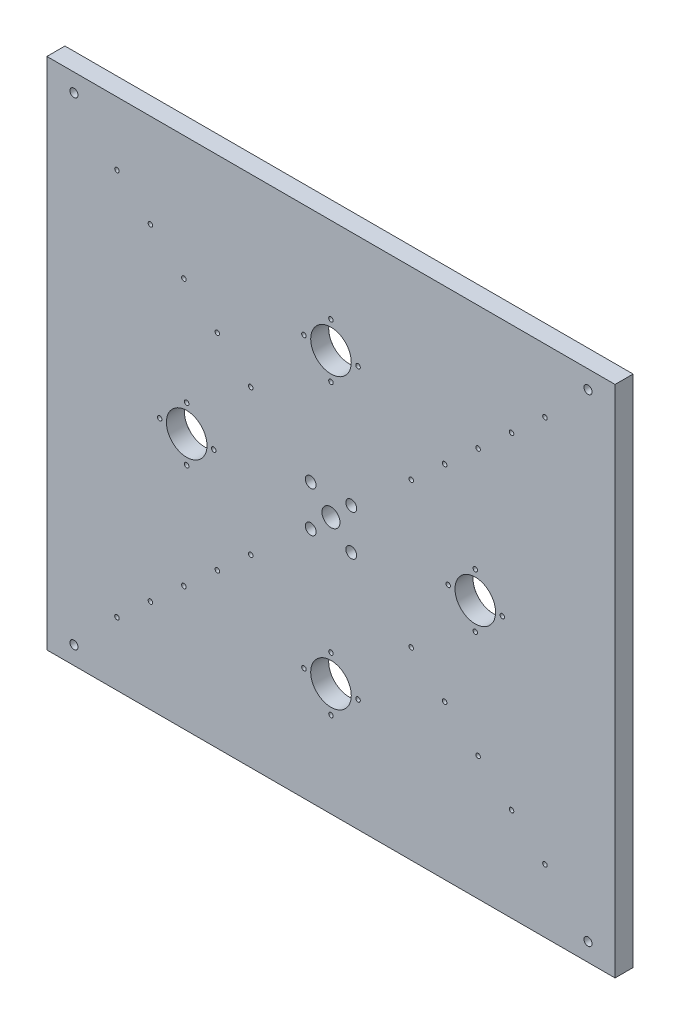
SolidWorks part; units mm, degrees
ref_plane "前视基准面" through (0, 0, 0) normal (0, 0, 1) x (1, 0, 0)
ref_plane "上视基准面" through (0, 0, 0) normal (0, 1, 0) x (1, 0, 0)
ref_plane "右视基准面" through (0, 0, 0) normal (1, 0, 0) x (0, 0, -1)
sketch "草图1" plane through (0, 0, 0) normal (0, 0, 1) x (1, 0, 0)
  line L1 (-315, 285) -> (315, 285)
  line L2 (-315, 285) -> (-315, -285)
  line L3 (-315, -285) -> (315, -285)
  line L4 (315, 285) -> (315, -285)
  line L5 (-315, 285) -> (315, -285) construction
  line L6 (-315, -285) -> (315, 285) construction
  point P0 (0, 0)
  dimension "D1" = 630
  dimension "D2" = 570
extrude "凸台-拉伸1" add sketch "草图1" along normal blind 20
hole_wizard "大小mm 暗销槽口2" positions "草图2" profile "草图3" size "Ø20.0" standard "GB" slot yes
sketch "草图2" plane through (0, 0, 0) normal (0, 0, -1) x (-1, 0, 0)
  point P0 (0, 0)
sketch "草图3" plane through (0, 0, 0) normal (1, 0, 0) x (0, 1, 0)
  line L0 (0, 0) -> (0, 26.0086)
  line L1 (0, 26.0086) -> (10, 20)
  line L2 (10, 20) -> (10, 0.025)
  line L3 (10, 0.025) -> (10.025, 0)
  line L5 (10.025, 0) -> (0, 0)
  line L6 (-10, 0.025) -> (-10.025, 0) construction
  line L10 (0, 26.0086) -> (-10, 20) construction
  line L11 (0, -6.35) -> (0, 107.95) construction
  dimension "孔直径" = 20
  dimension "孔深度" = 20
  dimension "近端锥形沉头孔直径" = 20.05
  dimension "近端锥形沉头孔角度" = 90
  dimension "导头角度" = 118
sketch "草图4" plane through (0, 0, 0) normal (0, 0, -1) x (-1, 0, 0)
  line L0 (-315, -285) -> (315, 285) construction
  line L1 (-22.5, 22.5) -> (22.5, 22.5)
  line L2 (-22.5, 22.5) -> (-22.5, -22.5)
  line L3 (-22.5, -22.5) -> (22.5, -22.5)
  line L4 (22.5, 22.5) -> (22.5, -22.5)
  line L5 (-22.5, 22.5) -> (22.5, -22.5) construction
  line L6 (-22.5, -22.5) -> (22.5, 22.5) construction
  line L7 (-315, 285) -> (315, -285) construction
  line L8 (315, -285) -> (-315, -285) construction
  line L9 (315, 285) -> (315, -285) construction
  line L10 (-237.2914, -214.6923) -> (-88.9843, -80.5096)
  line L11 (-160, 0) -> (160, 0) construction
  line L12 (0, 160) -> (0, -160) construction
  line L13 (-237.2914, 214.6923) -> (-88.9843, 80.5096)
  line L14 (237.2914, -214.6923) -> (88.9843, -80.5096)
  line L15 (237.2914, 214.6923) -> (88.9843, 80.5096)
  line L16 (-160, 0) -> (0, -160)
  line L17 (-285, 265) -> (285, 265)
  line L18 (-285, 265) -> (-285, -265)
  line L19 (-285, -265) -> (285, -265)
  line L20 (285, 265) -> (285, -265)
  line L21 (-285, 265) -> (285, -265) construction
  line L22 (-285, -265) -> (285, 265) construction
  line L23 (-160, 0) -> (0, 160)
  line L24 (0, -160) -> (160, 0)
  line L25 (0, 160) -> (160, 0)
  circle A0 centre (160, 0) radius 30
  circle A1 centre (0, -160) radius 30
  point P0 (0, 0)
  point P8 (160, 30)
  point P25 (-200.2147, -181.1466)
  point P26 (-163.1379, -147.6009)
  point P27 (-126.0611, -114.0553)
  point P28 (130, 0)
  point P30 (-126.0611, 114.0553)
  point P31 (-163.1379, 147.6009)
  point P32 (-200.2147, 181.1466)
  point P35 (126.0611, -114.0553)
  point P36 (163.1379, -147.6009)
  point P37 (200.2147, -181.1466)
  point P40 (200.2147, 181.1466)
  point P41 (163.1379, 147.6009)
  point P42 (126.0611, 114.0553)
  point P43 (0, 0)
  point P51 (160, -30)
  point P52 (190, 0)
  point P53 (0, -130)
  point P55 (-30, -160)
  point P56 (0, -190)
  point P57 (30, -160)
  point P58 (-26.9315, -173.2172)
  dimension "D2" = 60
  dimension "D9" = 60
  dimension "D1" = 45
  dimension "D3" = 50
  dimension "D4" = 120
  dimension "D5" = 570
  dimension "D6" = 530
  dimension "D7" = 160
  dimension "D8" = 0
  dimension "D10" = 0
hole_wizard "打孔尺寸(%根据)内六角圆柱头螺钉的类型1" positions "3D草图1" profile "草图5" counterbore size "M8" standard "GB"
sketch3d "3D草图1"
  point P0 (285, 265, 0)
  point P3 (-285, 265, 0)
  point P6 (-285, -265, 0)
  point P9 (285, -265, 0)
sketch "草图5" plane through (285, 265, 0) normal (1, 0, 0) x (0, 1, 0)
  line L0 (0, 0) -> (0, 22.7039)
  line L1 (0, 22.7039) -> (4.5, 20)
  line L2 (4.5, 20) -> (4.5, 9)
  line L3 (4.5, 9) -> (7.5, 9)
  line L5 (7.5, 9) -> (7.5, 0.025)
  line L6 (7.5, 0.025) -> (7.525, 0)
  line L7 (7.525, 0) -> (0, 0)
  line L8 (-7.5, 0.025) -> (-7.525, 0) construction
  line L10 (0, 22.7039) -> (-4.5, 20) construction
  line L11 (0, -6.35) -> (0, 107.95) construction
  dimension "孔直径" = 9
  dimension "孔深度" = 20
  dimension "锥形沉头孔直径" = 15
  dimension "锥形沉头孔深度" = 9
  dimension "近端锥形沉头孔直径" = 15.05
  dimension "近端锥形沉头孔角度" = 90
  dimension "导头角度" = 118
hole_wizard "M6 螺纹孔1" positions "3D草图2" profile "草图6" tap size "M6" standard "GB"
sketch3d "3D草图2"
  point P0 (237.2914, -214.6923, 0)
  point P3 (200.2147, -181.1466, 0)
  point P6 (163.1379, -147.6009, 0)
  point P9 (126.0611, -114.0553, 0)
  point P12 (88.9843, -80.5096, 0)
sketch "草图6" plane through (237.2914, -214.6923, 0) normal (1, 0, 0) x (0, 1, 0)
  line L0 (0, 0) -> (0, 31.5022)
  line L1 (0, 31.5022) -> (2.5, 30)
  line L2 (2.5, 30) -> (2.5, 0.525)
  line L3 (2.5, 0.525) -> (3.025, 0)
  line L5 (3.025, 0) -> (0, 0)
  line L6 (-2.5, 0.525) -> (-3.025, 0) construction
  line L10 (0, 31.5022) -> (-2.5, 30) construction
  line L11 (0, -6.35) -> (0, 107.95) construction
  dimension "螺纹孔钻头直径" = 5
  dimension "螺纹孔钻头深度" = 30
  dimension "近端锥形沉头孔直径" = 6.05
  dimension "近端锥形沉头孔角度" = 90
  dimension "导头角度" = 118
cosmetic thread "孔螺蚊线1" parameters "D1"=12, "D2"=6
cosmetic thread "孔螺蚊线2" parameters "D1"=12, "D2"=6
cosmetic thread "孔螺蚊线3" parameters "D1"=12, "D2"=6
cosmetic thread "孔螺蚊线4" parameters "D1"=12, "D2"=6
cosmetic thread "孔螺蚊线5" parameters "D1"=12, "D2"=6
mirror "镜向1" about plane through (0, 0, 0) normal (1, 0, 0) of "M6 螺纹孔1"
cosmetic thread "孔螺蚊线6" parameters "D1"=12, "D2"=6
cosmetic thread "孔螺蚊线7" parameters "D1"=12, "D2"=6
cosmetic thread "孔螺蚊线8" parameters "D1"=12, "D2"=6
cosmetic thread "孔螺蚊线9" parameters "D1"=12, "D2"=6
cosmetic thread "孔螺蚊线10" parameters "D1"=12, "D2"=6
mirror "镜向2" about plane through (0, 0, 0) normal (0, 1, 0) of "M6 螺纹孔1", "镜向1"
cosmetic thread "孔螺蚊线11" parameters "D1"=12, "D2"=6
cosmetic thread "孔螺蚊线12" parameters "D1"=12, "D2"=6
cosmetic thread "孔螺蚊线13" parameters "D1"=12, "D2"=6
cosmetic thread "孔螺蚊线14" parameters "D1"=12, "D2"=6
cosmetic thread "孔螺蚊线15" parameters "D1"=12, "D2"=6
cosmetic thread "孔螺蚊线16" parameters "D1"=12, "D2"=6
cosmetic thread "孔螺蚊线17" parameters "D1"=12, "D2"=6
cosmetic thread "孔螺蚊线18" parameters "D1"=12, "D2"=6
cosmetic thread "孔螺蚊线19" parameters "D1"=12, "D2"=6
cosmetic thread "孔螺蚊线20" parameters "D1"=12, "D2"=6
hole_wizard "大小mm 暗销槽口4" positions "草图7" profile "草图8" size "Ø12.0" standard "GB" slot yes
sketch "草图7" plane through (0, 0, 0) normal (0, 0, -1) x (-1, 0, 0)
  point P0 (22.5, 22.5)
  point P3 (22.5, -22.5)
  point P6 (-22.5, -22.5)
  point P9 (-22.5, 22.5)
sketch "草图8" plane through (-22.5, 22.5, 0) normal (1, 0, 0) x (0, 1, 0)
  line L0 (0, 0) -> (0, 25.6052)
  line L1 (0, 25.6052) -> (6, 22)
  line L2 (6, 22) -> (6, 0.025)
  line L3 (6, 0.025) -> (6.025, 0)
  line L5 (6.025, 0) -> (0, 0)
  line L6 (-6, 0.025) -> (-6.025, 0) construction
  line L10 (0, 25.6052) -> (-6, 22) construction
  line L11 (0, -6.35) -> (0, 107.95) construction
  dimension "孔直径" = 12
  dimension "孔深度" = 22
  dimension "近端锥形沉头孔直径" = 12.05
  dimension "近端锥形沉头孔角度" = 90
  dimension "导头角度" = 118
hole_wizard "大小mm 暗销孔1" positions "3D草图3" profile "草图9" hole size "Ø1.0" standard "GB"
sketch3d "3D草图3"
  point P0 (160, 0, 0)
  point P3 (0, 160, 0)
  point P6 (-160, 0, 0)
  point P9 (0, -160, 0)
sketch "草图9" plane through (160, 0, 0) normal (1, 0, 0) x (0, 1, 0)
  line L0 (0, 0) -> (0, 38.0194)
  line L1 (0, 38.0194) -> (22.5, 24.5)
  line L2 (22.5, 24.5) -> (22.5, 0.05)
  line L3 (22.5, 0.05) -> (22.55, 0)
  line L5 (22.55, 0) -> (0, 0)
  line L6 (-22.5, 0.05) -> (-22.55, 0) construction
  line L10 (0, 38.0194) -> (-22.5, 24.5) construction
  line L11 (0, -6.35) -> (0, 107.95) construction
  dimension "孔直径" = 45
  dimension "孔深度" = 24.5
  dimension "近端锥形沉头孔直径" = 45.1
  dimension "近端锥形沉头孔角度" = 90
  dimension "导头角度" = 118
hole_wizard "M6 螺纹孔2" positions "3D草图4" profile "草图10" tap size "M6" standard "GB"
sketch3d "3D草图4"
  point P0 (-160, 30, 0)
  point P3 (-190, 0, 0)
  point P6 (-160, -30, 0)
  point P9 (-130, 0, 0)
sketch "草图10" plane through (-160, 30, 0) normal (1, 0, 0) x (0, 1, 0)
  line L0 (0, 0) -> (0, 21.5022)
  line L1 (0, 21.5022) -> (2.5, 20)
  line L2 (2.5, 20) -> (2.5, 0.525)
  line L3 (2.5, 0.525) -> (3.025, 0)
  line L5 (3.025, 0) -> (0, 0)
  line L6 (-2.5, 0.525) -> (-3.025, 0) construction
  line L10 (0, 21.5022) -> (-2.5, 20) construction
  line L11 (0, -6.35) -> (0, 107.95) construction
  dimension "螺纹孔钻头直径" = 5
  dimension "螺纹孔钻头深度" = 20
  dimension "近端锥形沉头孔直径" = 6.05
  dimension "近端锥形沉头孔角度" = 90
  dimension "导头角度" = 118
cosmetic thread "孔螺蚊线25" parameters "D1"=12, "D2"=6
cosmetic thread "孔螺蚊线26" parameters "D1"=12, "D2"=6
cosmetic thread "孔螺蚊线27" parameters "D1"=12, "D2"=6
cosmetic thread "孔螺蚊线28" parameters "D1"=12, "D2"=6
mirror "镜向3" about plane through (0, 0, 0) normal (1, 0, 0) of "M6 螺纹孔2"
cosmetic thread "孔螺蚊线29" parameters "D1"=12, "D2"=6
cosmetic thread "孔螺蚊线30" parameters "D1"=12, "D2"=6
cosmetic thread "孔螺蚊线31" parameters "D1"=12, "D2"=6
cosmetic thread "孔螺蚊线32" parameters "D1"=12, "D2"=6
hole_wizard "M6 螺纹孔3" positions "3D草图5" profile "草图11" tap size "M6" standard "GB"
sketch3d "3D草图5"
  point P0 (0, -130, 0)
  point P3 (-30, -160, 0)
  point P6 (0, -190, 0)
  point P9 (30, -160, 0)
sketch "草图11" plane through (0, -130, 0) normal (1, 0, 0) x (0, 1, 0)
  line L0 (0, 0) -> (0, 21.5022)
  line L1 (0, 21.5022) -> (2.5, 20)
  line L2 (2.5, 20) -> (2.5, 0.525)
  line L3 (2.5, 0.525) -> (3.025, 0)
  line L5 (3.025, 0) -> (0, 0)
  line L6 (-2.5, 0.525) -> (-3.025, 0) construction
  line L10 (0, 21.5022) -> (-2.5, 20) construction
  line L11 (0, -6.35) -> (0, 107.95) construction
  dimension "螺纹孔钻头直径" = 5
  dimension "螺纹孔钻头深度" = 20
  dimension "近端锥形沉头孔直径" = 6.05
  dimension "近端锥形沉头孔角度" = 90
  dimension "导头角度" = 118
cosmetic thread "孔螺蚊线33" parameters "D1"=12, "D2"=6
cosmetic thread "孔螺蚊线34" parameters "D1"=12, "D2"=6
cosmetic thread "孔螺蚊线35" parameters "D1"=12, "D2"=6
cosmetic thread "孔螺蚊线36" parameters "D1"=12, "D2"=6
mirror "镜向4" about plane through (0, 0, 0) normal (0, 1, 0) of "M6 螺纹孔3"
cosmetic thread "孔螺蚊线37" parameters "D1"=12, "D2"=6
cosmetic thread "孔螺蚊线38" parameters "D1"=12, "D2"=6
cosmetic thread "孔螺蚊线39" parameters "D1"=12, "D2"=6
cosmetic thread "孔螺蚊线40" parameters "D1"=12, "D2"=6
